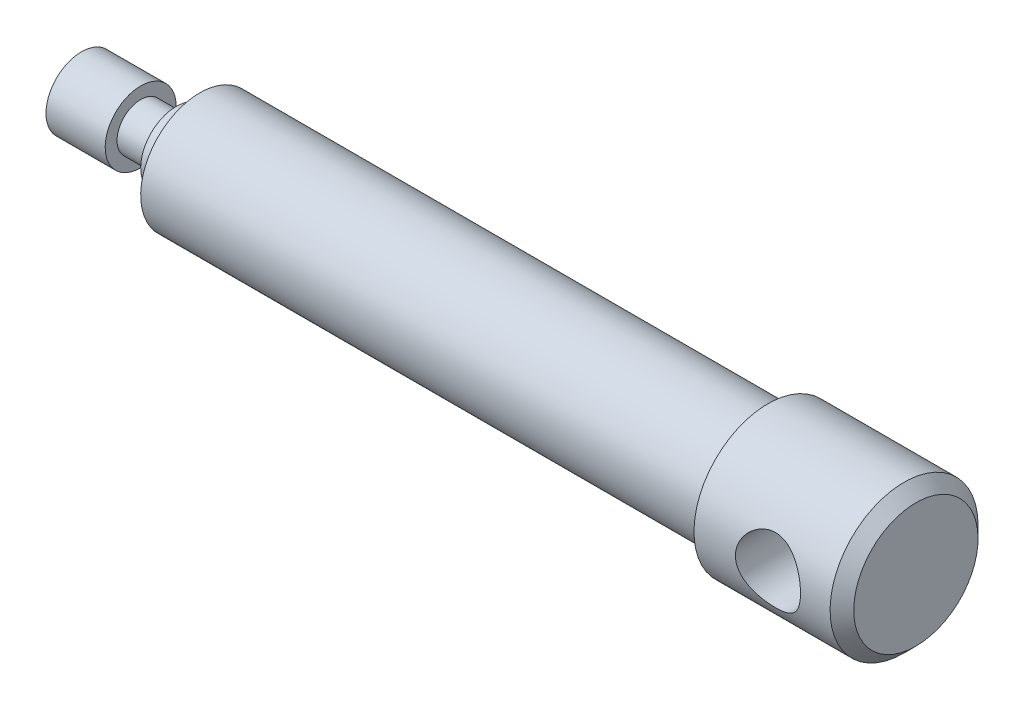
SolidWorks part; units mm, degrees
ref_plane "Front Plane" through (0, 0, 0) normal (0, 0, 1) x (1, 0, 0)
ref_plane "Top Plane" through (0, 0, 0) normal (0, 1, 0) x (1, 0, 0)
ref_plane "Right Plane" through (0, 0, 0) normal (1, 0, 0) x (0, 0, -1)
sketch "Sketch1" plane through (0, 0, 0) normal (0, 0, 1) x (1, 0, 0)
  line L1 (-12.5, 10) -> (-108.5, 10)
  line L2 (12.5, 0) -> (-12.5, 0)
  line L3 (12.5, 0) -> (12.5, 12.5)
  line L4 (12.5, 12.5) -> (-12.5, 12.5)
  line L5 (-12.5, 0) -> (-12.5, 12.5)
  line L6 (-108.5, 10) -> (-108.5, 0)
  line L7 (-108.5, 0) -> (-12.5, 0)
  line L8 (-108.5, 6) -> (-112.5, 6)
  line L9 (-112.5, 6) -> (-112.5, 0)
  line L10 (-112.5, 0) -> (-108.5, 0)
  line L11 (-112.5, 4) -> (-118.5, 4)
  line L12 (-118.5, 4) -> (-118.5, 0)
  line L13 (-118.5, 0) -> (-112.5, 0)
  line L14 (-118.5, 4) -> (-118.5, 6)
  line L15 (-118.5, 6) -> (-128.5, 6)
  line L16 (-128.5, 6) -> (-128.5, 0)
  line L17 (-128.5, 0) -> (-118.5, 0)
  line L18 (-128.5, 6) -> (-131.9641, 0)
  line L19 (-131.9641, 0) -> (-128.5, 0)
  line L20 (12.5, 0) -> (-131.9641, 0)
  point P7 (0, 0)
  dimension "D1" = 12.5
  dimension "D2" = 25
  dimension "D3" = 96
  dimension "D4" = 10
  dimension "D5" = 4
  dimension "D6" = 6
  dimension "D7" = 6
  dimension "D8" = 4
  dimension "D9" = 10
  dimension "D10" = 6
  dimension "D11" = 60
revolve "Revolve3" add sketch "Sketch1" angle 360 about L7
sketch "Sketch2" plane through (0, 0, 0) normal (0, 0, 1) x (1, 0, 0)
  circle A0 centre (0, 0) radius 5.5
  dimension "D1" = 11
extrude "Cut-Extrude1" cut sketch "Sketch2" against normal mid plane 30
chamfer "Chamfer1" distance 2 angle 45 1 edges at (12.5, -12.5, 0)
